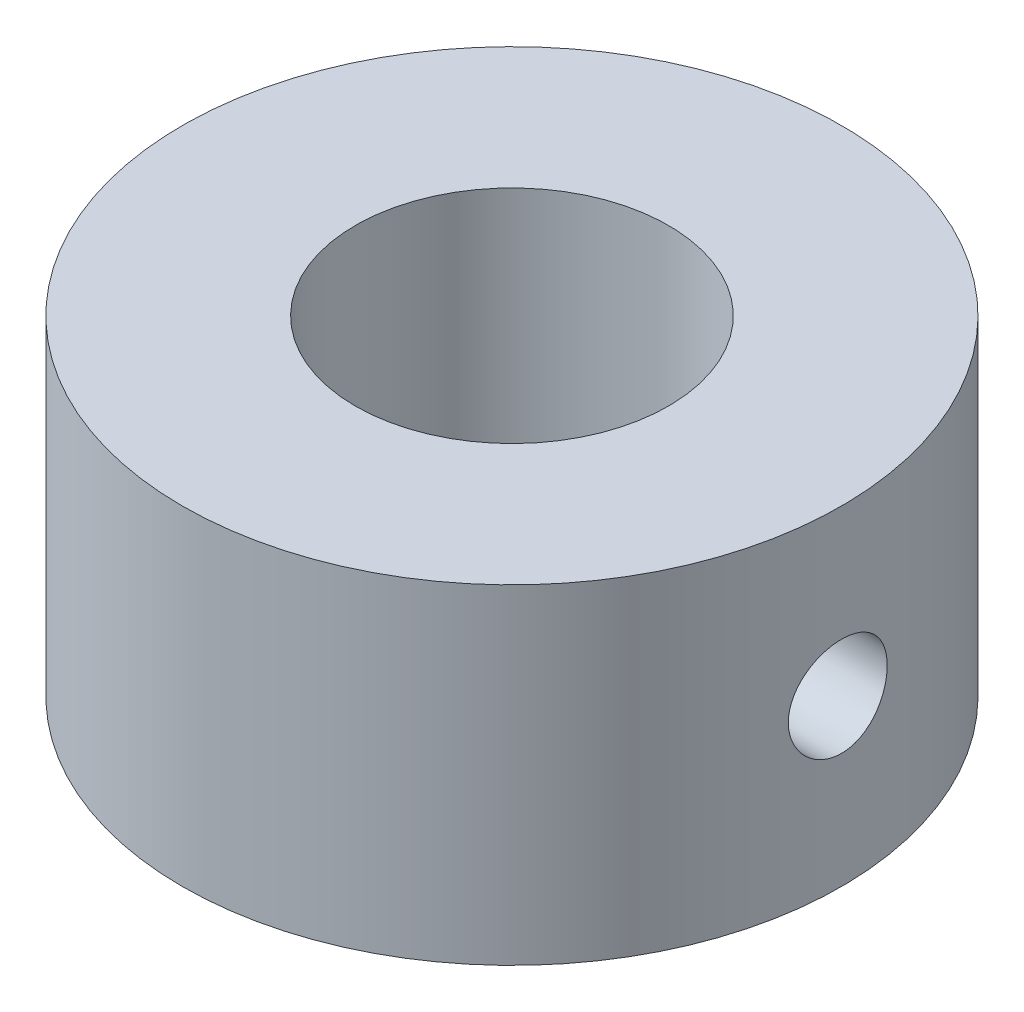
SolidWorks part; units mm, degrees
ref_plane "Front Plane" through (0, 0, 0) normal (0, 0, 1) x (1, 0, 0)
ref_plane "Top Plane" through (0, 0, 0) normal (0, 1, 0) x (1, 0, 0)
ref_plane "Right Plane" through (0, 0, 0) normal (1, 0, 0) x (0, 0, -1)
sketch "Sketch1" plane through (0, 0, 0) normal (0, 1, 0) x (1, 0, 0)
  circle A0 centre (0, 0) radius 4.75
  circle A1 centre (0, 0) radius 10
extrude "Boss-Extrude1" add sketch "Sketch1" along normal blind 10
ref_plane "Plane1" through (10, 0, 0) normal (1, 0, 0) x (0, 0, -1)
sketch "Sketch2" plane through (10, 0, 0) normal (1, 0, 0) x (0, 0, -1)
  line L0 (0, 0) -> (0, 10)
  line L1 (4.75, 10) -> (-4.75, 10) construction
  circle A0 centre (0, 5) radius 1.5
extrude "Cut-Extrude1" cut sketch "Sketch2" against normal blind 10 contours L0 A0 | L0 A0
